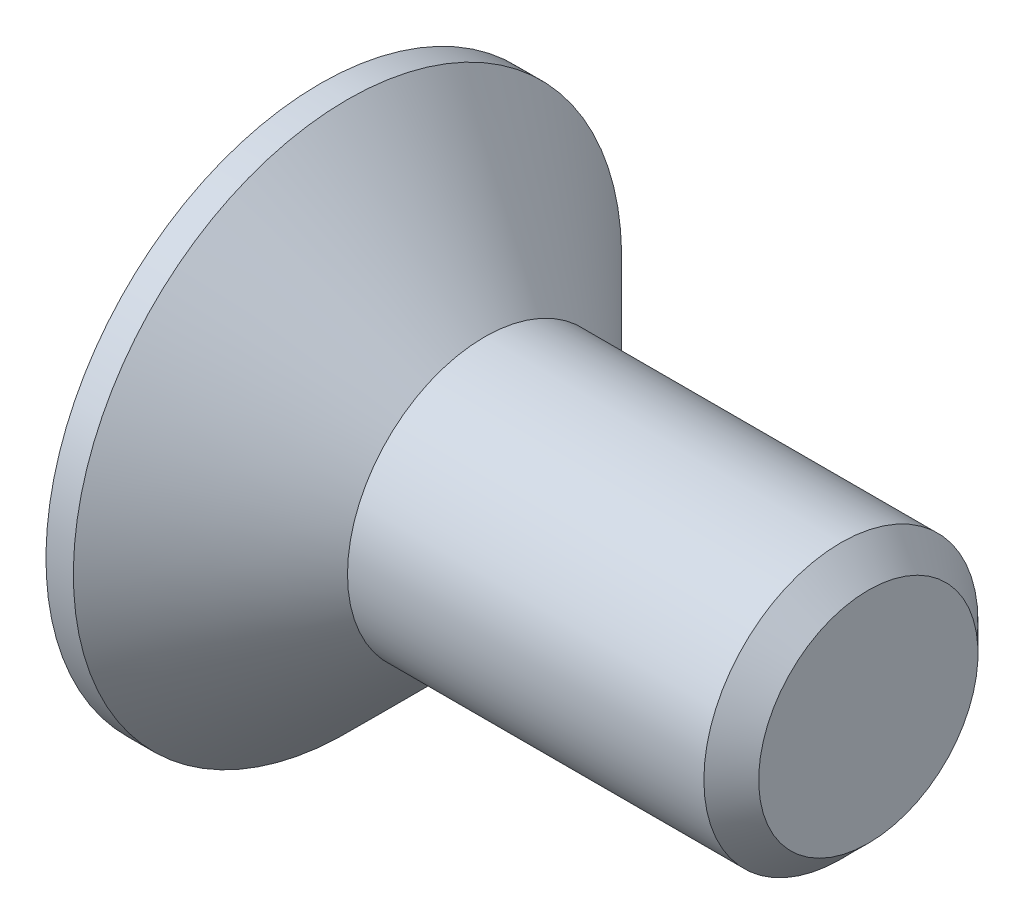
SolidWorks part; units mm, degrees
ref_plane "Plan de face" through (0, 0, 0) normal (0, 0, 1) x (1, 0, 0)
ref_plane "Plan de dessus" through (0, 0, 0) normal (0, 1, 0) x (1, 0, 0)
ref_plane "Plan de droite" through (0, 0, 0) normal (1, 0, 0) x (0, 0, -1)
sketch "Esquisse1" plane through (0, 0, 0) normal (0, 0, 1) x (1, 0, 0)
  line L0 (0, 0) -> (0, 5)
  line L1 (0, 5) -> (0.5, 5)
  line L2 (0.5, 5) -> (3, 2.5)
  line L3 (3, 2.5) -> (10, 2.5)
  line L4 (10, 2.5) -> (10, 0)
  line L5 (10, 0) -> (0, 0) construction
  line L6 (0, 0) -> (10, 0)
  dimension "D1" = 3
  dimension "D2" = 10
  dimension "D3" = 5
  dimension "D4" = 10
  dimension "D5" = 45
revolve "Révolution1" add sketch "Esquisse1" angle 360 about L5
chamfer "Chanfrein1" distance 0.5 angle 45 1 edges at (10, 2.5, 0)
sketch "Esquisse2" plane through (0, 0, 0) normal (-1, 0, 0) x (0, 0, 1)
  line L1 (0, 1.7321) -> (-1.5, 0.866)
  line L2 (-1.5, 0.866) -> (-1.5, -0.866)
  line L3 (-1.5, -0.866) -> (0, -1.7321)
  line L4 (0, -1.7321) -> (1.5, -0.866)
  line L5 (1.5, -0.866) -> (1.5, 0.866)
  line L6 (1.5, 0.866) -> (0, 1.7321)
  circle A0 centre (0, 0) radius 1.5 construction
  dimension "D1" = 3
extrude "Enlèv. mat.-Extru.1" cut sketch "Esquisse2" against normal blind 2.3
